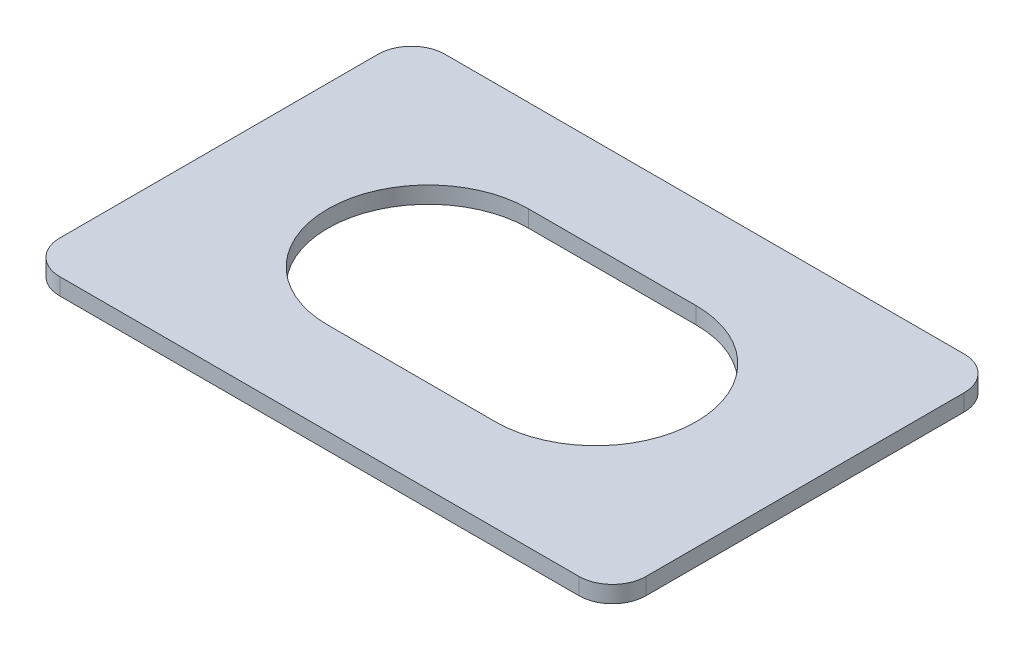
SolidWorks part; units mm, degrees
material "Медь"
ref_plane "Front" through (0, 0, 0) normal (0, 0, 1) x (1, 0, 0)
ref_plane "Top" through (0, 0, 0) normal (0, 1, 0) x (1, 0, 0)
ref_plane "Right" through (0, 0, 0) normal (1, 0, 0) x (0, 0, -1)
sketch "Эскиз1" plane through (0, 0, 0) normal (0, 1, 0) x (1, 0, 0)
  line L0 (0, 6) -> (0, 11.5) construction
  line L1 (15.5, -11.5) -> (-15.5, -11.5)
  line L2 (17.5, -9.5) -> (17.5, 9.5)
  line L3 (15.5, 11.5) -> (-15.5, 11.5)
  line L4 (-17.5, -9.5) -> (-17.5, 9.5)
  line L5 (17.5, -11.5) -> (0, 0) construction
  line L6 (17.5, 11.5) -> (0, 0) construction
  line L7 (-5, 6) -> (5, 6)
  line L8 (5, -6) -> (-5, -6)
  line L9 (0, 0) -> (-17.5, 11.5) construction
  line L10 (0, 0) -> (-17.5, -11.5) construction
  arc A0 (-5, 6) -> (-5, -6) centre (-5, 0) ccw
  arc A1 (5, 6) -> (5, -6) centre (5, 0) cw
  arc A2 (15.5, -11.5) -> (17.5, -9.5) centre (15.5, -9.5) ccw
  arc A3 (17.5, 9.5) -> (15.5, 11.5) centre (15.5, 9.5) ccw
  arc A4 (-15.5, -11.5) -> (-17.5, -9.5) centre (-15.5, -9.5) cw
  arc A5 (-15.5, 11.5) -> (-17.5, 9.5) centre (-15.5, 9.5) ccw
  point P0 (0, 0)
  dimension "D3" = 12
  dimension "D6" = 2
  dimension "D1" = 23
  dimension "D2" = 35
  dimension "D4" = 5
  dimension "D5" = 11.5
extrude "Бобышка-Вытянуть1" add sketch "Эскиз1" along normal blind 1
